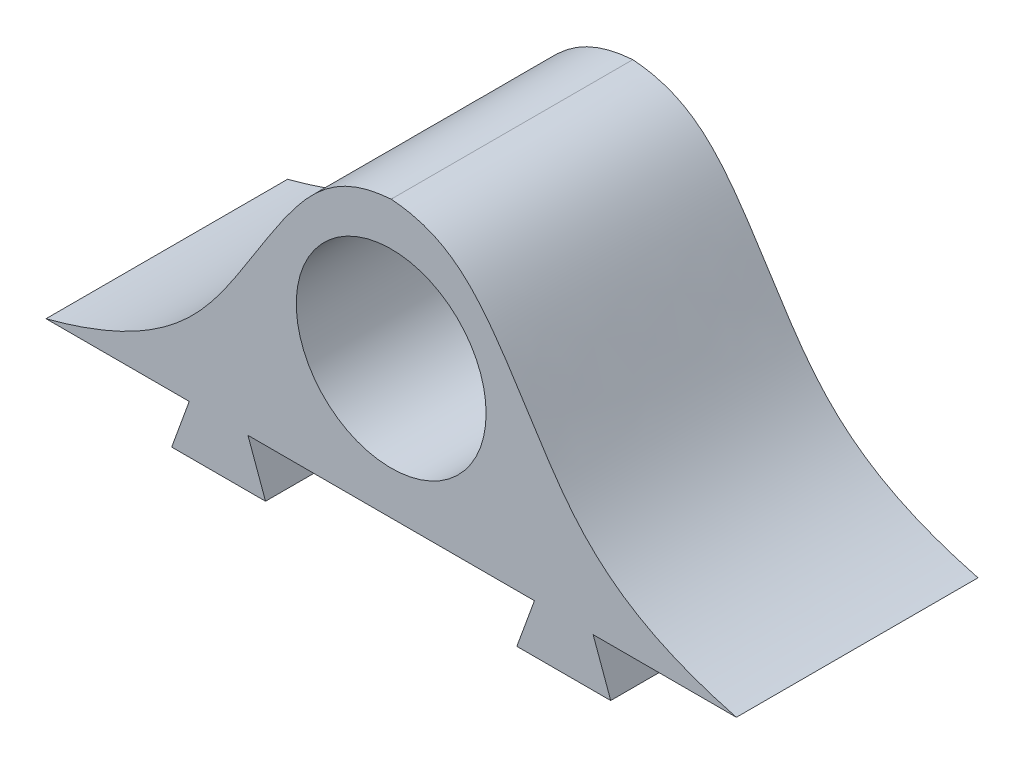
SolidWorks part; units mm, degrees
ref_plane "前基準面" through (0, 0, 0) normal (0, 0, 1) x (1, 0, 0)
ref_plane "上基準面" through (0, 0, 0) normal (0, 1, 0) x (1, 0, 0)
ref_plane "右基準面" through (0, 0, 0) normal (1, 0, 0) x (0, 0, -1)
sketch "草圖1" plane through (0, 0, 0) normal (0, 0, 1) x (1, 0, 0)
  line L0 (0, 11.1445) -> (0, -12.5978) construction
  line L1 (-10, 0) -> (-5.85, 0)
  line L3 (-5.85, 0) -> (-6.3596, -1.4)
  line L4 (-6.3596, -1.4) -> (-3.6404, -1.4)
  line L5 (-5, 0.8048) -> (-5, -2.2157) construction
  line L6 (5, 0.8048) -> (5, -2.2157) construction
  line L7 (-4.15, 0) -> (-3.6404, -1.4)
  line L8 (-4.15, 0) -> (4.15, 0)
  line L9 (4.15, 0) -> (3.6404, -1.4)
  line L13 (6.3596, -1.4) -> (3.6404, -1.4)
  line L14 (-4, 6.4147) -> (-4, -1.6919) construction
  line L15 (5.85, 0) -> (6.3596, -1.4)
  line L16 (5.85, 0) -> (10, 0)
  circle A0 centre (0, 4) radius 2.75
  spline S0 degree 3 poles (-10, 0) (-6.5066, 0.9147) (-5.1424, 2.7597) (-2.7009, 6.6543) (-1.7466, 7.8689) (0, 8) knots 0 0 0 0 0.426506 0.526506 1 1 1 1
  spline S1 degree 3 poles (10, 0) (6.5066, 0.9147) (5.1424, 2.7597) (2.7009, 6.6543) (1.7466, 7.8689) (0, 8) knots 0 0 0 0 0.426506 0.526506 1 1 1 1
  point P19 (-5, -1.4)
  dimension "D2" = 5.5
  dimension "D5" = 20
  dimension "D3" = 4
  dimension "D4" = 4
  dimension "D6" = 1.4
  dimension "D7" = 70
  dimension "D8" = 1.7
  dimension "D9" = 10
  dimension "D11" = 8
extrude "填料-伸長1" add sketch "草圖1" along normal blind 7
sketch "草圖2" plane through (0, 0, 0) normal (1, 0, 0) x (0, 0, -1)
  line L0 (-7, -1.4) -> (-7, 0) construction
  line L2 (-7, -1.4) -> (0, -1.4) construction
  line L3 (-1.9, -1.4) -> (-1.1, -1.4)
  line L5 (-1.5, -2.1441) -> (-1.5, -0.3009) construction
  arc A1 (-1.1, -1.4) -> (-1.9, -1.4) centre (-1.5, -1.9217) ccw
  dimension "D2" = 0.8
  dimension "D1" = 5.5
extrude "除料-伸長1" cut sketch "草圖2" against normal mid plane 13
